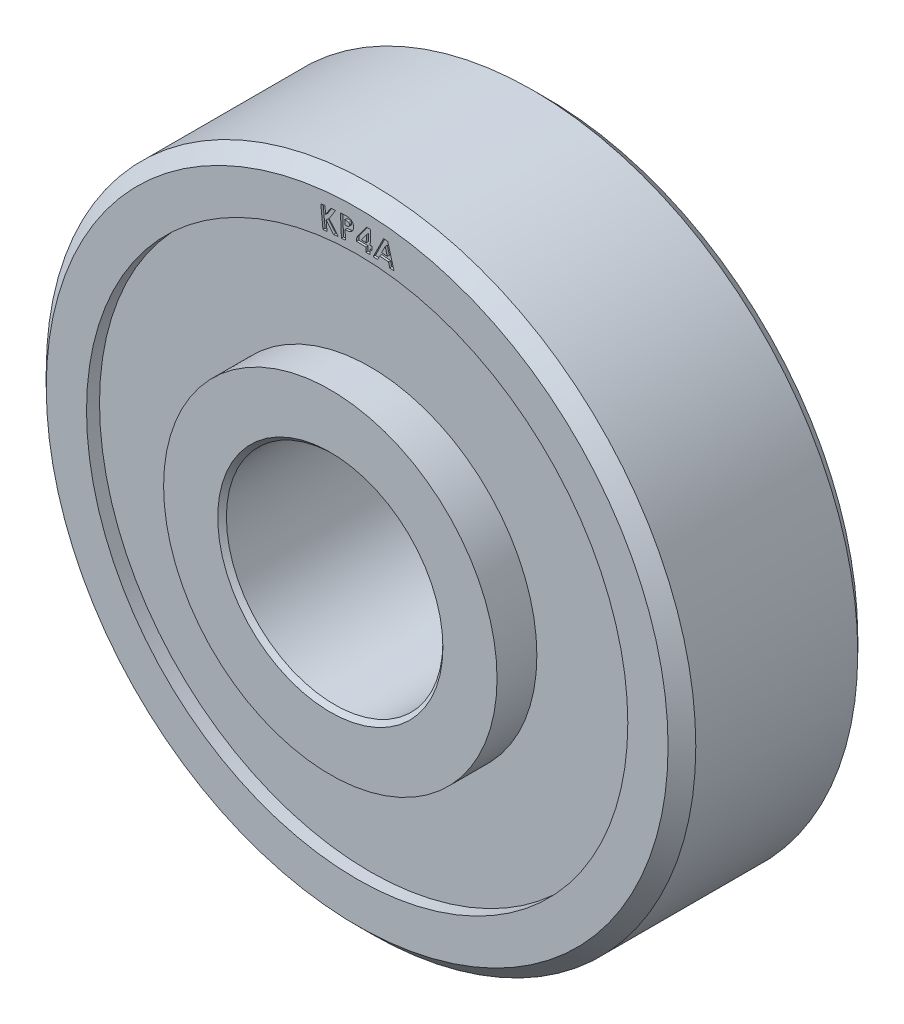
SolidWorks part; units mm, degrees
ref_plane "Front Plane" through (0, 0, 0) normal (0, 0, 1) x (1, 0, 0)
ref_plane "Top Plane" through (0, 0, 0) normal (0, 1, 0) x (1, 0, 0)
ref_plane "Right Plane" through (0, 0, 0) normal (1, 0, 0) x (0, 0, -1)
sketch "Sketch1" plane through (0, 0, 0) normal (1, 0, 0) x (0, 0, -1)
  line L0 (0, 0) -> (8.5758, 0) construction
  line L1 (-3.5687, 3.302) -> (-3.5687, 4.8895)
  line L2 (-3.5687, 4.8895) -> (-2.4003, 4.8895)
  line L3 (-2.4003, 4.8895) -> (-2.4003, 7.9375)
  line L4 (-2.4003, 7.9375) -> (-2.7813, 7.9375)
  line L5 (-2.7813, 7.9375) -> (-2.7813, 9.1186)
  line L6 (-2.7813, 9.1186) -> (-2.3749, 9.525)
  line L7 (-2.3749, 9.525) -> (2.3749, 9.525)
  line L8 (-3.4417, 3.175) -> (3.4417, 3.175)
  line L9 (0, 0) -> (0, 12.798) construction
  line L10 (2.7813, 9.1186) -> (2.3749, 9.525)
  line L11 (2.7813, 7.9375) -> (2.7813, 9.1186)
  line L12 (2.4003, 7.9375) -> (2.7813, 7.9375)
  line L13 (2.4003, 4.8895) -> (2.4003, 7.9375)
  line L14 (3.5687, 4.8895) -> (2.4003, 4.8895)
  line L15 (3.5687, 3.302) -> (3.5687, 4.8895)
  line L16 (3.4417, 3.175) -> (3.5687, 3.302)
  line L17 (-3.5687, 3.302) -> (-3.4417, 3.175)
  point P3 (-3.5687, 3.175)
  point P19 (3.5687, 3.175)
  dimension "D1" = 6.35
  dimension "D2" = 9.779
  dimension "D3" = 7.1374
  dimension "D4" = 5.5626
  dimension "D5" = 0.381
  dimension "D6" = 15.875
  dimension "D7" = 45
  dimension "D8" = 0.4064
  dimension "D9" = 19.05
revolve "Revolve1" add sketch "Sketch1" angle 360 about L0
sketch "Sketch2" plane through (0, 0, 2.7813) normal (0, 0, 1) x (1, 0, 0)
  line L0 (0, 0) -> (0, 8.128) construction
  arc A1 (-1.0763, 8.0564) -> (1.0763, 8.0564) centre (0, 0) cw construction
  text T0 "KP4A" font "Century Gothic" height 0.635
  dimension "D1" = 8.128
  dimension "D2" = 2.159
extrude "Cut-Extrude1" cut sketch "Sketch2" against normal blind 0.0635
